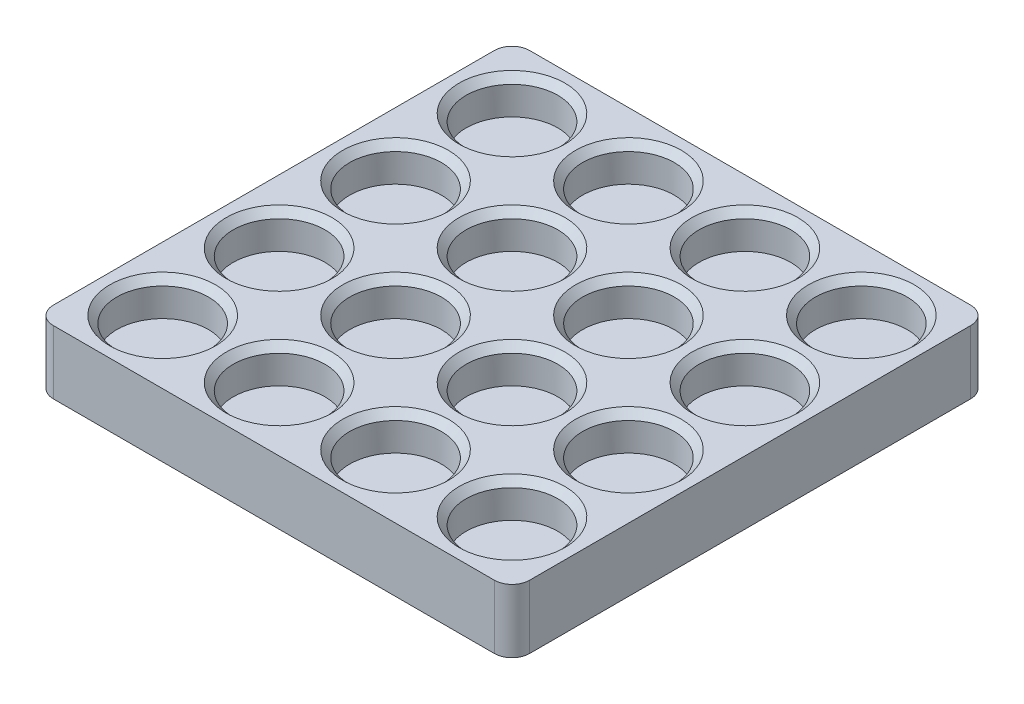
SolidWorks part; units mm, degrees
ref_plane "Front Plane" through (0, 0, 0) normal (0, 0, 1) x (1, 0, 0)
ref_plane "Top Plane" through (0, 0, 0) normal (0, 1, 0) x (1, 0, 0)
ref_plane "Right Plane" through (0, 0, 0) normal (1, 0, 0) x (0, 0, -1)
sketch "Sketch1" plane through (0, 0, 0) normal (0, 1, 0) x (1, 0, 0)
  line L1 (-67.5, -67.5) -> (67.5, -67.5)
  line L2 (-67.5, -67.5) -> (-67.5, 67.5)
  line L3 (-67.5, 67.5) -> (67.5, 67.5)
  line L4 (67.5, -67.5) -> (67.5, 67.5)
  line L5 (-67.5, -67.5) -> (67.5, 67.5) construction
  line L6 (-67.5, 67.5) -> (67.5, -67.5) construction
  point P0 (0, 0)
  dimension "D1" = 135
extrude "Boss-Extrude1" add sketch "Sketch1" along normal blind 18
fillet "Fillet1" radius 5 4 edges at (-67.5, 9, -67.5) (-67.5, 9, 67.5) (67.5, 9, -67.5) (67.5, 9, 67.5)
sketch "Sketch2" plane through (0, 18, 0) normal (0, 1, 0) x (1, 0, 0)
  line L0 (0, -1000) -> (0, 49000) construction
  line L1 (-1000, 0) -> (49000, 0) construction
  line L2 (-49.5, 49.5) -> (-49.5, 16.5) construction
  line L3 (-49.5, 16.5) -> (-16.5, 16.5) construction
  line L4 (-16.5, 16.5) -> (-16.5, 49.5) construction
  line L5 (-16.5, 49.5) -> (-49.5, 49.5) construction
  circle A0 centre (-49.5, 49.5) radius 13
  circle A1 centre (49.5, 49.5) radius 13
  circle A2 centre (49.5, -49.5) radius 13
  circle A3 centre (-49.5, -49.5) radius 13
  circle A4 centre (-16.5, 49.5) radius 13
  circle A5 centre (16.5, 49.5) radius 13
  circle A6 centre (-16.5, 16.5) radius 13
  circle A7 centre (-49.5, 16.5) radius 13
  circle A8 centre (-16.5, -49.5) radius 13
  circle A9 centre (-49.5, -16.5) radius 13
  circle A10 centre (-16.5, -16.5) radius 13
  circle A11 centre (49.5, 16.5) radius 13
  circle A12 centre (16.5, 16.5) radius 13
  circle A13 centre (49.5, -16.5) radius 13
  circle A14 centre (16.5, -16.5) radius 13
  circle A15 centre (16.5, -49.5) radius 13
  dimension "D1" = 26
  dimension "D2" = 33
  dimension "D3" = 99
  dimension "D4" = 33
extrude "Cut-Extrude1" cut sketch "Sketch2" against normal blind 10
chamfer "Chamfer1" distance 2 angle 45 16 edges at (49.5, 18, 62.5) (16.5, 18, 62.5) (-16.5, 18, 36.5) (-49.5, 18, 36.5) (49.5, 18, 29.5) (16.5, 18, 29.5) (-16.5, 18, 3.5) (-49.5, 18, 3.5) (-49.5, 18, -3.5) (-16.5, 18, -3.5) (16.5, 18, -29.5) (49.5, 18, -29.5) (49.5, 18, -62.5) (-49.5, 18, -36.5) (-16.5, 18, -36.5) (16.5, 18, -62.5)
